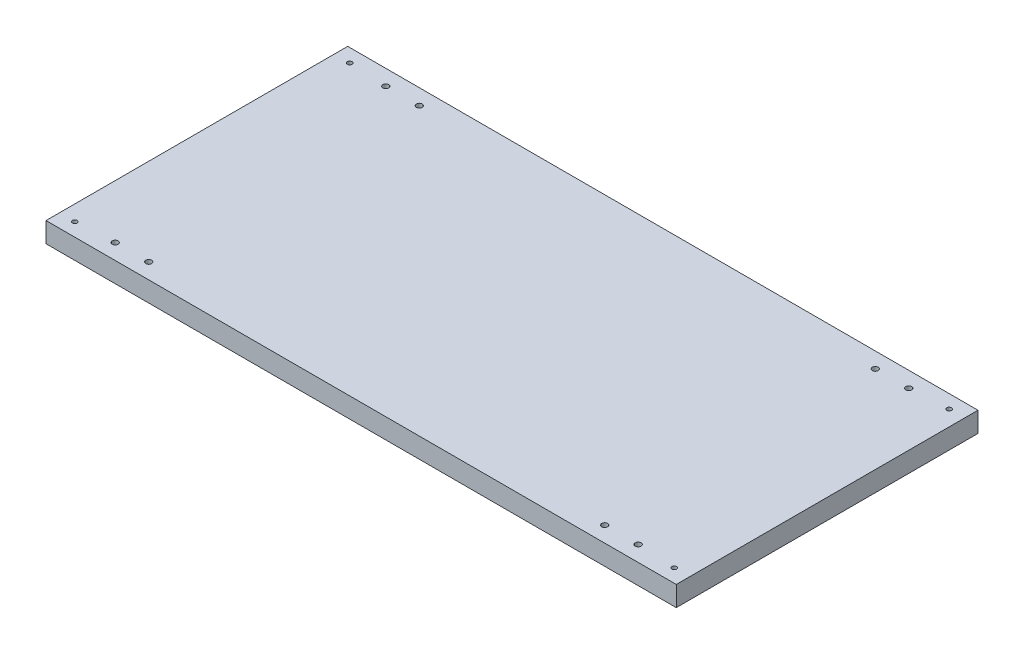
SolidWorks part; units mm, degrees
ref_plane "Front Plane" through (0, 0, 0) normal (0, 0, 1) x (1, 0, 0)
ref_plane "Top Plane" through (0, 0, 0) normal (0, 1, 0) x (1, 0, 0)
ref_plane "Right Plane" through (0, 0, 0) normal (1, 0, 0) x (0, 0, -1)
sketch "Sketch2" plane through (0, 0, 0) normal (0, 1, 0) x (1, 0, 0)
  line L0 (-223.5, 132.4222) -> (-223.5, -126.6646) construction
  line L1 (-235, 112.5) -> (235, 112.5)
  line L2 (-235, 112.5) -> (-235, -112.5)
  line L3 (-235, -112.5) -> (235, -112.5)
  line L4 (235, 112.5) -> (235, -112.5)
  line L5 (-235, 112.5) -> (235, -112.5) construction
  line L6 (-235, -112.5) -> (235, 112.5) construction
  line L7 (223.5, 123.0896) -> (223.5, -131.9348) construction
  circle A0 centre (223.5, 102.5) radius 1.75
  circle A1 centre (223.5, -102.5) radius 1.75
  circle A2 centre (-223.5, -102.5) radius 1.75
  circle A3 centre (-223.5, 102.5) radius 1.75
  point P0 (0, 0)
  dimension "D6" = 3.5
  dimension "D1" = 470
  dimension "D2" = 225
  dimension "D3" = 11.5
  dimension "D4" = 11.5
  dimension "D5" = 10
  dimension "D7" = 10
  dimension "D8" = 10
  dimension "D9" = 10
extrude "Boss-Extrude1" add sketch "Sketch2" along normal blind 15
sketch "Sketch3" plane through (0, 15, 0) normal (0, 1, 0) x (1, 0, 0)
  line L0 (-235, 112.5) -> (-235, -112.5) construction
  line L1 (235, 112.5) -> (-235, 112.5) construction
  line L2 (235, -112.5) -> (235, 112.5) construction
  circle A0 centre (-195, 100.9) radius 2.2
  circle A1 centre (-170, 100.9) radius 2.2
  circle A2 centre (195, 100.9) radius 2.2
  circle A3 centre (170, 100.9099) radius 2.2
  dimension "D1" = 4.4
  dimension "D5" = 4.4
  dimension "D2" = 40
  dimension "D3" = 11.6
  dimension "D6" = 11.6
  dimension "D7" = 40
  dimension "D4" = 2
  dimension "D8" = 2
extrude "Cut-Extrude1" cut sketch "Sketch3" against normal through all
sketch "Sketch4" plane through (0, 15, 0) normal (0, 1, 0) x (1, 0, 0)
  line L0 (-235, -112.5) -> (235, -112.5) construction
  line L1 (-235, 112.5) -> (-235, -112.5) construction
  line L2 (235, -112.5) -> (235, 112.5) construction
  circle A0 centre (-195, -100.9) radius 2.2
  circle A1 centre (-195, 100.9) radius 2.2 construction
  circle A2 centre (195, -100.9) radius 2.2
  circle A3 centre (195, 100.9) radius 2.2 construction
  circle A4 centre (-170, -100.9) radius 2.2
  circle A6 centre (170, -100.9) radius 2.2
  circle A7 centre (-220, -100.9) radius 2.2 [skipped]
  dimension "D1" = 11.6
  dimension "D2" = 40
  dimension "D3" = 40
  dimension "D4" = 11.6
  dimension "D7" = 25
  dimension "D5" = 2
  dimension "D6" = 2
extrude "Cut-Extrude2" cut sketch "Sketch4" against normal through all
